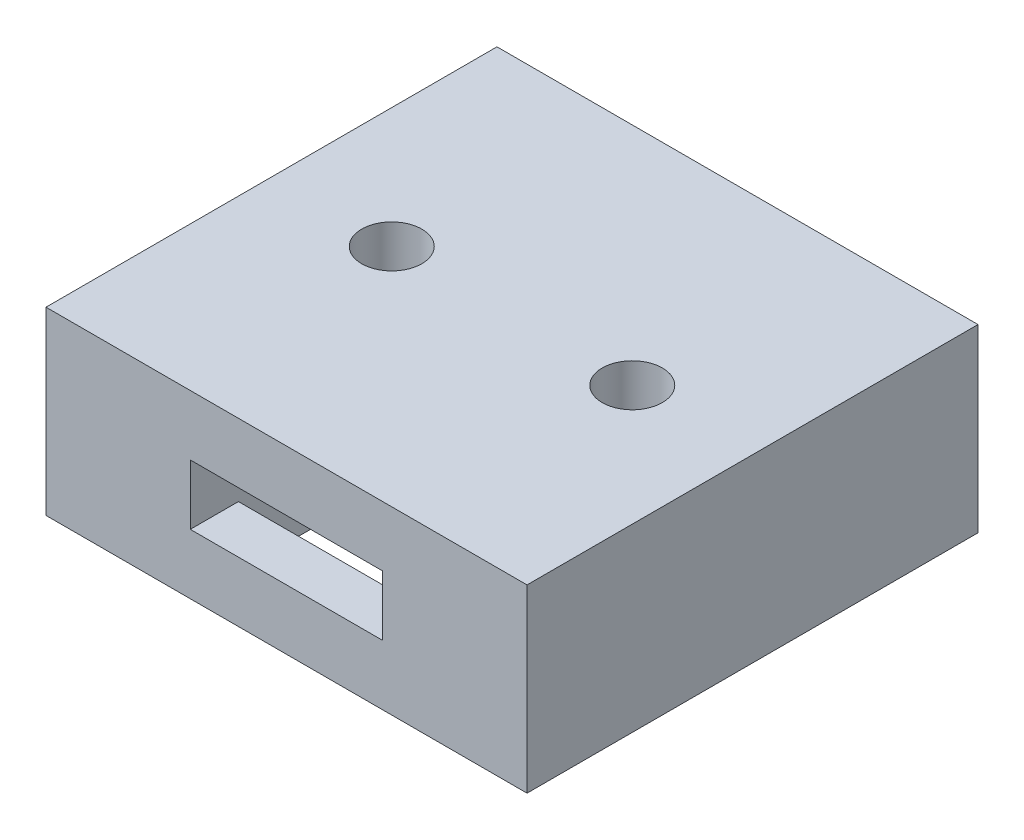
SolidWorks part; units mm, degrees
ref_plane "Front Plane" through (0, 0, 0) normal (0, 0, 1) x (1, 0, 0)
ref_plane "Top Plane" through (0, 0, 0) normal (0, 1, 0) x (1, 0, 0)
ref_plane "Right Plane" through (0, 0, 0) normal (1, 0, 0) x (0, 0, -1)
sketch "Croquis1" plane through (0, 0, 0) normal (0, 1, 0) x (1, 0, 0)
  line L0 (8, 7.5) -> (-8, 7.5)
  line L1 (8, 7.5) -> (8, -7.5)
  line L2 (8, -7.5) -> (-8, -7.5)
  line L3 (-8, 7.5) -> (-8, -7.5)
  line L4 (8, 7.5) -> (-8, -7.5) construction
  line L5 (8, -7.5) -> (-8, 7.5) construction
  circle A3 centre (4, 0) radius 1
  circle A4 centre (-4, 0) radius 1
  point P0 (0, 0)
  dimension "D1" = 7.5
  dimension "D6" = 2
  dimension "D7" = 2
  dimension "D2" = 15
  dimension "D3" = 16
  dimension "D4" = 7.5
  dimension "D5" = 4
  dimension "D8" = 4
extrude "Saliente-Extruir1" add sketch "Croquis1" along normal blind 6
sketch "Croquis2" plane through (0, 6, 0) normal (0, 1, 0) x (1, 0, 0)
  line L0 (-8, -7.5) -> (8, -7.5)
  line L1 (8, -7.5) -> (8, 7.5)
  line L2 (8, 7.5) -> (-8, 7.5)
  line L3 (-8, 7.5) -> (-8, -7.5)
  line L4 (10, -9.5) -> (10, 9.5)
  line L5 (10, -9.5) -> (-10, -9.5)
  line L6 (10, 9.5) -> (-10, 9.5)
  line L7 (-10, -9.5) -> (-10, 9.5)
  line L8 (10, -9.5) -> (-10, 9.5) construction
  line L9 (10, 9.5) -> (-10, -9.5) construction
  line L10 (-8.4, -7.9) -> (-8.4, 7.9)
  line L11 (-8.4, -7.9) -> (8.4, -7.9)
  line L12 (-8.4, 7.9) -> (8.4, 7.9)
  line L13 (8.4, -7.9) -> (8.4, 7.9)
  line L14 (-8.4, -7.9) -> (8.4, 7.9) construction
  line L15 (-8.4, 7.9) -> (8.4, -7.9) construction
  point P9 (0, 0)
  point P10 (0, 0)
  dimension "D1" = 2
  dimension "D2" = 2
  dimension "D3" = 0.4
  dimension "D4" = 0.4
  dimension "D5" = 8
  dimension "D6" = 7.5
sketch "Croquis6" plane through (0, 6, 0) normal (0, 1, 0) x (1, 0, 0)
  line L0 (3.2, -4.9) -> (3.2, -2.9)
  line L1 (3.2, -4.9) -> (-3.2, -4.9)
  line L2 (3.2, -2.9) -> (-3.2, -2.9)
  line L3 (-3.2, -4.9) -> (-3.2, -2.9)
  line L4 (3.2, -4.9) -> (-3.2, -2.9) construction
  line L5 (3.2, -2.9) -> (-3.2, -4.9) construction
  line L6 (3.2, 4.9) -> (-3.2, 4.9)
  line L7 (3.2, 4.9) -> (3.2, 2.9)
  line L8 (-3.2, 4.9) -> (-3.2, 2.9)
  line L9 (3.2, 2.9) -> (-3.2, 2.9)
  line L10 (3.2, 4.9) -> (-3.2, 2.9) construction
  line L11 (-3.2, 4.9) -> (3.2, 2.9) construction
  line L14 (-8, -7.5) -> (8, -7.5) construction
  line L16 (8, 7.5) -> (-8, 7.5) construction
  point P1 (0, -3.9)
  point P2 (0, 3.9)
  dimension "D1" = 6.4
  dimension "D2" = 6.4
  dimension "D3" = 2
  dimension "D4" = 2
  dimension "D5" = 3.6
  dimension "D6" = 3.6
extrude "Cortar-Extruir3" cut sketch "Croquis6" against normal blind 32
sketch "Croquis7" plane through (0, 0, 7.5) normal (0, 0, -1) x (-1, 0, 0)
  line L0 (3.2, 2) -> (-3.2, 2)
  line L1 (3.2, 2) -> (3.2, 4)
  line L2 (-3.2, 2) -> (-3.2, 4)
  line L3 (3.2, 4) -> (-3.2, 4)
  line L4 (3.2, 2) -> (-3.2, 4) construction
  line L5 (-3.2, 2) -> (3.2, 4) construction
  line L7 (8, 6) -> (-8, 6) construction
  point P1 (0, 3)
  point P13 (0, 6)
  dimension "D1" = 6.4
  dimension "D2" = 2
  dimension "D3" = 2
extrude "Cortar-Extruir4" cut sketch "Croquis7" along normal blind 4.6
mirror "Simetría1" about plane through (0, 0, 0) normal (0, 0, 1) of "Cortar-Extruir4", "Cortar-Extruir3"
sketch "Croquis8" plane through (0, 6, 0) normal (0, 1, 0) x (1, 0, 0)
  line L0 (-3.2, 4.9) -> (3.2, 4.9)
  line L1 (-3.2, 4.9) -> (-3.2, 2.9)
  line L2 (3.2, 4.9) -> (3.2, 2.9)
  line L3 (-3.2, 2.9) -> (3.2, 2.9)
  line L4 (-3.2, 4.9) -> (3.2, 2.9) construction
  line L5 (3.2, 4.9) -> (-3.2, 2.9) construction
  line L7 (0, 0) -> (3, 0) construction
  line L8 (-3.2, -4.9) -> (-3.2, -2.9)
  line L9 (3.2, -4.9) -> (3.2, -2.9)
  line L10 (-3.2, -4.9) -> (3.2, -4.9)
  line L11 (-3.2, -2.9) -> (3.2, -2.9)
  line L13 (8, -7.5) -> (8, 7.5) construction
  circle A0 centre (4, 0) radius 1 construction
  point P1 (0, 3.9)
  dimension "D1" = 2
  dimension "D2" = 6.4
  dimension "D3" = 3.9
  dimension "D4" = 4.8
extrude "Saliente-Extruir5" add sketch "Croquis8" against normal blind 2
chamfer "Chaflán1" distance 1 angle 45 2 edges at (0, 2, 4.9) (0, 2, -4.9)
